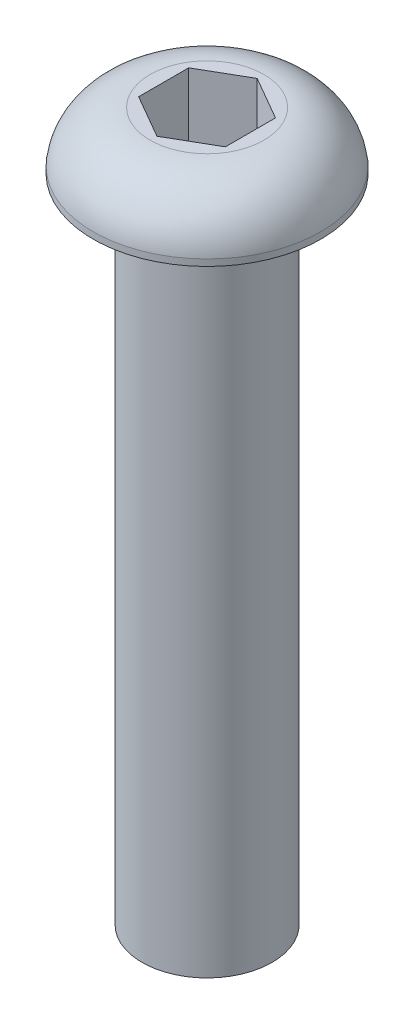
SolidWorks part; units mm, degrees
ref_plane "Plano frontal" through (0, 0, 0) normal (0, 0, 1) x (1, 0, 0)
ref_plane "Plano superior" through (0, 0, 0) normal (0, 1, 0) x (1, 0, 0)
ref_plane "Plano direito" through (0, 0, 0) normal (1, 0, 0) x (0, 0, -1)
sketch "Esboço1" plane through (0, 0, 0) normal (0, 0, 1) x (1, 0, 0)
  line L0 (0, 0) -> (0, 32.6421) construction
  line L1 (0, 32.6421) -> (2.625, 32.6421)
  line L2 (5.25, 30.3) -> (5.25, 30)
  line L3 (5.25, 30) -> (3, 30)
  line L4 (3, 30) -> (3, 0)
  line L5 (3, 0) -> (0, 0)
  line L6 (0, 0) -> (0, 32.6421)
  arc A0 (2.625, 32.6421) -> (5.25, 30.3) centre (2.625, 30) cw
  dimension "D1" = 10.5
  dimension "D2" = 6
  dimension "D3" = 5.25
  dimension "D4" = 0.3
  dimension "D5" = 30
revolve "Revolução1" add sketch "Esboço1" angle 360 about L0
sketch "Esboço2" plane through (0, 32.6421, 0) normal (0, 1, 0) x (1, 0, 0)
  line L1 (0, 2.3094) -> (-2, 1.1547)
  line L2 (-2, 1.1547) -> (-2, -1.1547)
  line L3 (-2, -1.1547) -> (0, -2.3094)
  line L4 (0, -2.3094) -> (2, -1.1547)
  line L5 (2, -1.1547) -> (2, 1.1547)
  line L6 (2, 1.1547) -> (0, 2.3094)
  circle A0 centre (0, 0) radius 2 construction
  dimension "D1" = 4
extrude "Corte-extrusão1" cut sketch "Esboço2" against normal blind 5
